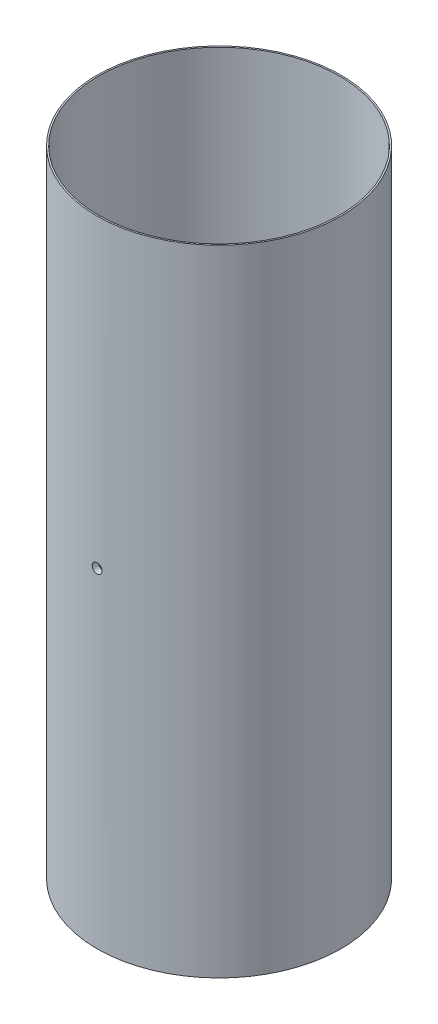
SolidWorks part; units mm, degrees
material "6061-T4 (SS)"
ref_plane "Front Plane" through (0, 0, 0) normal (0, 0, 1) x (1, 0, 0)
ref_plane "Top Plane" through (0, 0, 0) normal (0, 1, 0) x (1, 0, 0)
ref_plane "Right Plane" through (0, 0, 0) normal (1, 0, 0) x (0, 0, -1)
sketch "Sketch1" plane through (0, 0, 0) normal (0, 1, 0) x (1, 0, 0)
  circle A0 centre (0, 0) radius 63.5
  circle A1 centre (0, 0) radius 60.325
  dimension "D1" = 127
  dimension "D2" = 120.65
extrude "Boss-Extrude1" add sketch "Sketch1" along normal blind 330.2
sketch "Sketch5" plane through (0, 0, 0) normal (0, 1, 0) x (1, 0, 0)
  circle A0 centre (0, 0) radius 60.325
  circle A1 centre (0, 0) radius 62.7063
  dimension "D1" = 120.65
  dimension "D2" = 125.4125
extrude "Cut-Extrude1" cut sketch "Sketch5" along normal blind 158.75
sketch "Sketch6" plane through (0, 330.2, 0) normal (0, 1, 0) x (1, 0, 0)
  circle A0 centre (0, 0) radius 60.325
  circle A1 centre (0, 0) radius 62.7063
  dimension "D1" = 120.65
  dimension "D2" = 125.4125
extrude "Cut-Extrude2" cut sketch "Sketch6" against normal blind 120.65
ref_plane "Plane1" through (0, 0, 63.5) normal (0, 0, 1) x (1, 0, 0)
ref_plane "Plane2" through (0, 0, -63.5) normal (0, 0, 1) x (1, 0, 0)
sketch "Sketch8" plane through (0, 0, 63.5) normal (0, 0, 1) x (1, 0, 0)
  circle A0 centre (0, 171.45) radius 6.4556
  dimension "D1" = 171.45
sketch "Sketch12" plane through (0, 0, -63.5) normal (0, 0, 1) x (1, 0, 0)
  circle A0 centre (0, 171.45) radius 6.4556
hole_wizard "Tap Drill for 1/4-20 Tap8" positions "Sketch20" profile "Sketch19" hole size "1/4-20" standard "ANSI Inch"
sketch "Sketch20" plane through (0, 0, 63.5) normal (0, 0, 1) x (1, 0, 0)
  point P0 (0, 171.45)
sketch "Sketch19" plane through (0, 171.45, 63.5) normal (1, 0, 0) x (0, -1, 0)
  line L0 (0, 0) -> (0, 3.175)
  line L1 (0, 3.175) -> (2.5527, 3.175)
  line L2 (2.5527, 3.175) -> (2.5527, 0)
  line L5 (2.5527, 0) -> (0, 0)
  line L11 (0, -6.35) -> (0, 107.95) construction
  dimension "Thru Hole Dia." = 5.1054
  dimension "Thru Hole Depth" = 3.175
hole_wizard "Tap Drill for 1/4-20 Tap9" positions "Sketch21" profile "Sketch22" hole size "1/4-20" standard "ANSI Inch"
sketch "Sketch21" plane through (0, 0, -63.5) normal (0, 0, 1) x (1, 0, 0)
  point P0 (0, 171.45)
sketch "Sketch22" plane through (0, 171.45, -63.5) normal (1, 0, 0) x (0, 1, 0)
  line L0 (0, 0) -> (0, 3.175)
  line L1 (0, 3.175) -> (2.5527, 3.175)
  line L2 (2.5527, 3.175) -> (2.5527, 0)
  line L5 (2.5527, 0) -> (0, 0)
  line L11 (0, -6.35) -> (0, 107.95) construction
  dimension "Thru Hole Dia." = 5.1054
  dimension "Thru Hole Depth" = 3.175
ref_plane "Plane3" through (0, 313.5439, 0) normal (0, 1, 0) x (1, 0, 0)
sketch "Sketch24" plane through (0, 313.5439, 0) normal (0, 1, 0) x (1, 0, 0)
  circle A0 centre (0, 0) radius 60.325
sketch "Sketch25" plane through (0, 0, 0) normal (0, 0, 1) x (1, 0, 0)
  point P0 (0, 171.45)
sketch "Sketch28" plane through (0, 0, 0) normal (1, 0, 0) x (0, 0, -1)
  line L0 (0, 171.45) -> (-150.2291, 171.45) construction
  line L1 (-150.2291, 171.45) -> (0, 171.45) construction
  line L2 (0, 171.45) -> (137.0328, 171.45) construction
sketch "Sketch29" plane through (0, 0, 0) normal (0, 0, 1) x (1, 0, 0)
  line L0 (110.9363, 171.45) -> (-138.7821, 171.45) construction
ref_plane "Plane4" through (62.738, 0, 0) normal (1, 0, 0) x (0, 0, -1)
ref_plane "Plane5" through (-62.738, 0, 0) normal (1, 0, 0) x (0, 0, -1)
